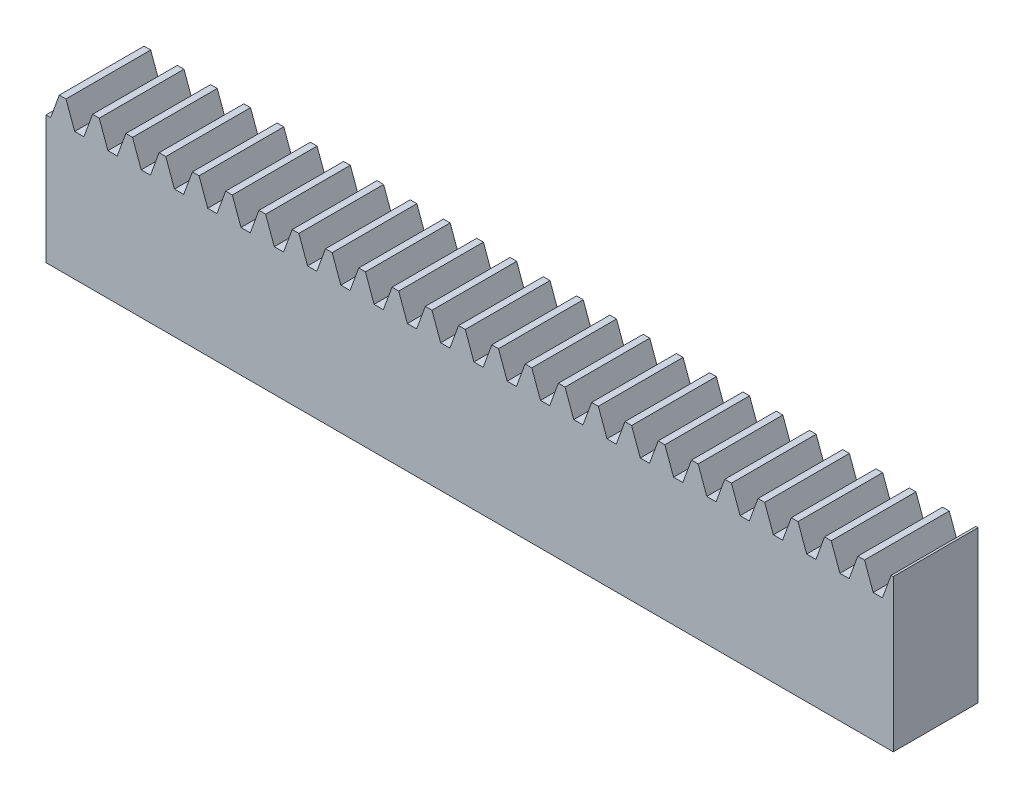
SolidWorks part; units mm, degrees
ref_plane "Plane1" through (0, 0, 0) normal (0, 0, 1) x (1, 0, 0)
ref_plane "Plane2" through (0, 0, 0) normal (0, 1, 0) x (1, 0, 0)
ref_plane "Plane3" through (0, 0, 0) normal (1, 0, 0) x (0, 0, -1)
sketch "HoldingSke" plane through (0, 0, 0) normal (0, 1, 0) x (1, 0, 0)
  line L0 (0, 0) -> (0.0928, 0.6602)
  line L1 (-15, 0) -> (100, 0) construction
  line L2 (0, 0) -> (-2.1039, 2.3779)
  line L3 (0, 0) -> (-11.863, 4.5341)
  line L4 (0, 0) -> (7.6947, 3.9206)
  line L5 (0, 0) -> (-23.7986, -8.8762)
  line L6 (0, 0) -> (-10.5278, -7.1032)
  line L9 (-71.009, 38.7566) -> (41.7541, 79.799)
  line L10 (-76.2, 3.8779) -> (-56.2, 3.8779)
  line L11 (0, 0) -> (-12, 0)
  line L12 (-76.2, 101.6) -> (-76.147, 101.6)
  line L13 (24.9733, 27.94) -> (52.9518, 28.4284)
  line L14 (24.9733, 27.94) -> (24.9743, 27.94)
  line L15 (24.9733, 27.94) -> (100.4006, 29.5858)
  circle A0 centre (0, 0) radius 19.05
  circle A1 centre (0, 0) radius 10
  circle A2 centre (0, 0) radius 12.7
  dimension "MPH" = 20
  dimension "Diameter" = 38.1
  dimension "Num_teeth" = 27
  dimension "Pitch" = 0.6667
  dimension "Width" = 12
  dimension "Show_teeth" = 998
  dimension "Thickness" = 12.7
  dimension "Ap" = 20
  dimension "Pitch_height" = 20
  dimension "Backlash" = 0.053
  dimension "Addendum_fac" = 1
  dimension "Dedendum_fac" = 1.25
  dimension "Clearance_fac" = 0.25
  dimension "Dedendum_add" = 0.001
  dimension "Length" = 120
  dimension "Module" = 1.5
sketch "BlankSke" plane through (0, 0, 0) normal (0, 0, 1) x (1, 0, 0)
  line L1 (0, 0) -> (120, 0)
  line L2 (0, 0) -> (0, 21.5)
  line L3 (0, 21.5) -> (120, 21.5)
  line L4 (120, 0) -> (120, 21.5)
  dimension "Length" = 120
  dimension "Blank_height" = 21.5
extrude "Blank" add sketch "BlankSke" against normal blind 12
sketch "TooCutSkeIll" plane through (0, 0, 0) normal (0, 0, 1) x (1, 0, 0)
  line L0 (-1.8687, 21.4605) -> (-0.7447, 18.3724)
  line L1 (-0.3914, 18.125) -> (0.3914, 18.125)
  line L2 (0.7447, 18.3724) -> (1.8687, 21.4605)
  line L3 (120, 21.5) -> (0, 21.5) construction
  line L4 (0, 0) -> (0, 64.897) construction
  line L5 (-13.208, 20) -> (12.954, 20) construction
  line L6 (0, 0) -> (120, 0) construction
  line L7 (1.3371, 20) -> (1.3371, 48.7463) construction
  line L8 (-1.3371, 20) -> (-1.3371, 48.7463) construction
  line L9 (1.9251, 21.5) -> (1.9251, 21.5254)
  line L10 (-1.9251, 21.5) -> (-1.9251, 21.5254)
  line L11 (-1.9251, 21.5254) -> (1.9251, 21.5254)
  arc A0 (0.3914, 18.125) -> (0.7447, 18.3724) centre (0.3914, 18.501) ccw
  arc A1 (-0.7447, 18.3724) -> (-0.3914, 18.125) centre (-0.3914, 18.501) ccw
  arc A2 (1.9251, 21.5) -> (1.8687, 21.4605) centre (1.9251, 21.44) ccw
  arc A3 (-1.8687, 21.4605) -> (-1.9251, 21.5) centre (-1.9251, 21.44) ccw
  dimension "Root_fillet" = 0.376
  dimension "Break_rad" = 0.06
  dimension "Pitch_height" = 20
  dimension "Gap_width" = 2.6742
  dimension "Dedendum" = 1.875
  dimension "Addendum_plus" = 1.5254
  dimension "Pressure_angle" = 20
extrude "ToothCutIll" [suppressed] cut sketch "TooCutSkeIll" against normal through all
sketch "TooCutSkeSim" plane through (0, 0, 0) normal (0, 0, 1) x (1, 0, 0)
  line L0 (0.6547, 18.125) -> (-0.6547, 18.125)
  line L1 (1.8923, 21.5254) -> (0.6547, 18.125)
  line L2 (0, 17.4625) -> (0, 53.467) construction
  line L3 (1.8923, 21.5254) -> (-1.8923, 21.5254)
  line L6 (-1.8923, 21.5254) -> (-0.6547, 18.125)
  line L9 (-1.3371, 20) -> (1.3371, 20) construction
  line L10 (0, 0) -> (120, 0) construction
  line L11 (1.3371, 20) -> (1.3371, 53.467) construction
  line L12 (-1.3371, 20) -> (-1.3371, 53.467) construction
  dimension "Pitch_height" = 20
  dimension "Pressure_angle" = 20
  dimension "Gap_width" = 2.6742
  dimension "Dedendum" = 1.875
  dimension "Addendum_plus" = 1.5254
extrude "ToothCutSim" cut sketch "TooCutSkeSim" against normal through all
pattern_linear "TeethCuts" count 26 spacing 4.7124 along (1, 0, 0) of "ToothCutIll", "ToothCutSim"
equation "' \"Module@HoldingSke\" = 6.35"
equation "' \"Num_teeth@HoldingSke\" = 12"
equation "' \"Ap@HoldingSke\" =  20"
equation "' \"Width@HoldingSke\" = 0.25 * 25.4"
equation "' \"Show_teeth@HoldingSke\" = 500"
equation "' \"Backlash@HoldingSke\" = 0.009 * 25.4"
equation "' \"Addendum_fac@HoldingSke\" = 1.0"
equation "' \"Dedendum_fac@HoldingSke\" = 1.25"
equation "' \"Dedendum_add@HoldingSke\" = 0.00005 * 25.4"
equation "' \"Clearance_fac@HoldingSke\" = 0.25"
equation "' \"Pitch_height@HoldingSke\" = 1 * 25.4"
equation "' \"Length@HoldingSke\" = 4.71 * 25.4"
equation "\"Pitch@HoldingSke\" = 1 / \"Module@HoldingSke\""
equation "\"MPH@HoldingSke\" = \"Dedendum_fac@HoldingSke\" / \"Pitch@HoldingSke\" + 2 * \"Dedendum_add@HoldingSke\" + 0.002 * 25.4"
equation "\"MPH@HoldingSke\" = ((sgn( \"MPH@HoldingSke\" - \"Pitch_height@HoldingSke\")+1)*( \"MPH@HoldingSke\" - \"Pitch_height@HoldingSke\"))/2 + \"Pitch_height@HoldingSke\""
equation "\"Blank_height@BlankSke\" = \"Pitch_height@HoldingSke\" + \"Addendum_fac@HoldingSke\"  / \"Pitch@HoldingSke\" "
equation "\"Length@BlankSke\" =  \"Length@HoldingSke\""
equation "\"Face_width@Blank\" = \"Width@HoldingSke\""
equation "\"Pressure_angle@TooCutSkeIll\" = \"Ap@HoldingSke\""
equation "\"Addendum_plus@TooCutSkeIll\" =  \"Addendum_fac@HoldingSke\"  / \"Pitch@HoldingSke\" + 0.001 *25.4"
equation "\"Dedendum@TooCutSkeIll\" = \"Dedendum_fac@HoldingSke\"  / \"Pitch@HoldingSke\""
equation "\"Pitch_height@TooCutSkeIll\" =  \"MPH@HoldingSke\""
equation "\"Gap_width@TooCutSkeIll\" = 3.14159265 / 2 / \"Pitch@HoldingSke\" + 6 * \"Backlash@HoldingSke\""
equation "\"Pressure_angle@TooCutSkeSim\" = \"Ap@HoldingSke\""
equation "\"Addendum_plus@TooCutSkeSim\" =  \"Addendum_fac@HoldingSke\"  / \"Pitch@HoldingSke\" + 0.001 * 25.4"
equation "\"Dedendum@TooCutSkeSim\" = \"Dedendum_fac@HoldingSke\"  / \"Pitch@HoldingSke\""
equation "\"Pitch_height@TooCutSkeSim\" =  \"MPH@HoldingSke\""
equation "\"Gap_width@TooCutSkeSim\" = 3.14159265 / 2 / \"Pitch@HoldingSke\" + 6 * \"Backlash@HoldingSke\""
equation "\"Root_fillet@TooCutSkeIll\" = \"Clearance_fac@HoldingSke\" / \"Pitch@HoldingSke\" + \"Dedendum_add@HoldingSke\""
equation "\"Break_rad@TooCutSkeIll\" = 0.02 / \"Pitch@HoldingSke\" * 2"
equation "\"Linear_pitch@TeethCuts\" = 3.14159265 / \"Pitch@HoldingSke\""
equation "\"Num_teeth@HoldingSke\" = int( ( \"Length@HoldingSke\" + 0 ) / (3.14159265 / \"Pitch@HoldingSke\")) + 0.9999  + 1"
equation " \"Num_teeth@TeethCuts\" = int( \"Show_teeth@HoldingSke\" ) + 1"
equation " \"Num_teeth@TeethCuts\" = ((sgn( \"Num_teeth@TeethCuts\" - \"Num_teeth@HoldingSke\" )-1)*( \"Num_teeth@TeethCuts\" - \"Num_teeth@HoldingSke\" ))/-2+ \"Num_teeth@HoldingSke\""
equation " \"Num_teeth@TeethCuts\" = ((sgn( \"Num_teeth@TeethCuts\" - 2.0)+1)*( \"Num_teeth@TeethCuts\" - 2.0))/2 +2.0"
